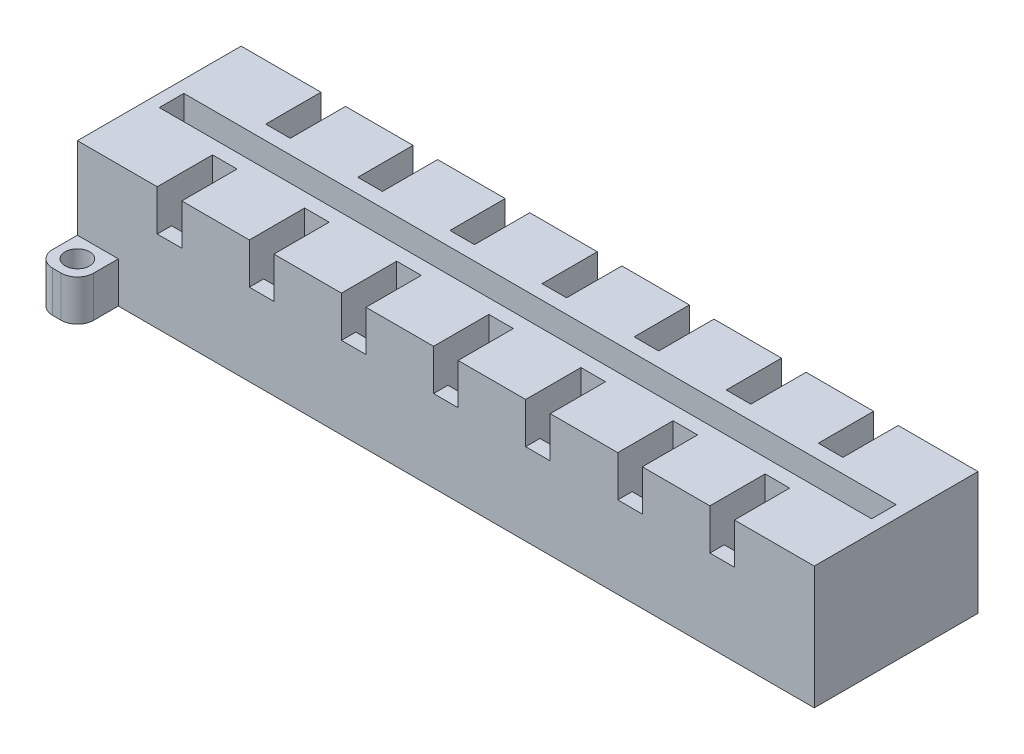
SolidWorks part; units mm, degrees
ref_plane "Front Plane" through (0, 0, 0) normal (0, 0, 1) x (1, 0, 0)
ref_plane "Top Plane" through (0, 0, 0) normal (0, 1, 0) x (1, 0, 0)
ref_plane "Right Plane" through (0, 0, 0) normal (1, 0, 0) x (0, 0, -1)
sketch "Sketch1" plane through (0, 0, 0) normal (0, 0, 1) x (1, 0, 0)
  line L1 (0, 0) -> (90, 0)
  line L2 (0, 0) -> (0, -20)
  line L3 (0, -20) -> (90, -20)
  line L4 (90, 0) -> (90, -20)
  dimension "D1" = 20
  dimension "D2" = 90
extrude "Boss-Extrude1" add sketch "Sketch1" along normal blind 20
sketch "Sketch2" plane through (0, 0, 0) normal (0, 1, 0) x (1, 0, 0)
  line L0 (0, -10) -> (90, -10) construction
  line L1 (0, -20) -> (0, 0) construction
  line L2 (90, -20) -> (90, 0) construction
  line L4 (0, -8.5) -> (90, -8.5)
  line L5 (0, -8.5) -> (0, -11.5)
  line L6 (0, -11.5) -> (90, -11.5)
  line L7 (90, -8.5) -> (90, -11.5)
  line L8 (0, -8.5) -> (90, -11.5) construction
  line L9 (0, -11.5) -> (90, -8.5) construction
  point P6 (45, -10)
  dimension "D1" = 3
extrude "Cut-Extrude1" cut sketch "Sketch2" against normal blind 10
sketch "Sketch3" plane through (0, 0, 0) normal (0, 1, 0) x (1, 0, 0)
  line L0 (45, 0) -> (45, -20) construction
  line L1 (90, 0) -> (0, 0) construction
  line L2 (90, -20) -> (0, -20) construction
  line L3 (45, -20) -> (90, -20) construction
  line L4 (90, -20) -> (90, 0) construction
  line L5 (90, 0) -> (45, 0) construction
  line L6 (45, 0) -> (0, 0) construction
  line L7 (0, 0) -> (0, -20) construction
  line L8 (0, -20) -> (45, -20) construction
  line L9 (45, -20) -> (22.5, -20) construction
  line L10 (22.5, -20) -> (22.5, 0) construction
  line L11 (22.5, 0) -> (67.5, 0) construction
  line L12 (67.5, 0) -> (67.5, -20) construction
  line L13 (22.5, 0) -> (0, 0) construction
  line L14 (0, 0) -> (11.25, 0) construction
  line L15 (11.25, 0) -> (11.25, -20) construction
  line L16 (11.25, -20) -> (22.5, -20) construction
  line L17 (22.5, -20) -> (45, -20) construction
  line L18 (45, -20) -> (33.75, -20) construction
  line L19 (33.75, -20) -> (33.75, 0) construction
  line L20 (33.75, 0) -> (45, 0) construction
  line L21 (45, 0) -> (67.5, 0) construction
  line L22 (67.5, 0) -> (56.25, 0) construction
  line L23 (56.25, 0) -> (56.25, -20) construction
  line L24 (56.25, -20) -> (67.5, -20) construction
  line L25 (67.5, -20) -> (90, -20) construction
  line L26 (78.75, -20) -> (78.75, 0) construction
  line L27 (0, -11.5) -> (0, -20) construction
  line L28 (0, -20) -> (0, -15.75) construction
  line L29 (0, -15.75) -> (90, -15.75) construction
  line L30 (90, -15.75) -> (90, 0) construction
  line L31 (90, 0) -> (90, -8.5) construction
  line L32 (90, -8.5) -> (90, -4.25) construction
  line L33 (90, -4.25) -> (0, -4.25) construction
  line L35 (9.75, -13.25) -> (12.75, -13.25)
  line L36 (9.75, -13.25) -> (9.75, -18.25)
  line L37 (9.75, -18.25) -> (12.75, -18.25)
  line L38 (12.75, -13.25) -> (12.75, -18.25)
  line L39 (9.75, -13.25) -> (12.75, -18.25) construction
  line L40 (9.75, -18.25) -> (12.75, -13.25) construction
  line L41 (21, -13.25) -> (24, -13.25)
  line L42 (21, -13.25) -> (21, -18.25)
  line L43 (21, -18.25) -> (24, -18.25)
  line L44 (24, -13.25) -> (24, -18.25)
  line L45 (21, -13.25) -> (24, -18.25) construction
  line L46 (21, -18.25) -> (24, -13.25) construction
  line L47 (32.25, -13.25) -> (35.25, -13.25)
  line L48 (32.25, -13.25) -> (32.25, -18.25)
  line L49 (32.25, -18.25) -> (35.25, -18.25)
  line L50 (35.25, -13.25) -> (35.25, -18.25)
  line L51 (32.25, -13.25) -> (35.25, -18.25) construction
  line L52 (32.25, -18.25) -> (35.25, -13.25) construction
  line L53 (43.5, -13.25) -> (46.5, -13.25)
  line L54 (43.5, -13.25) -> (43.5, -18.25)
  line L55 (43.5, -18.25) -> (46.5, -18.25)
  line L56 (46.5, -13.25) -> (46.5, -18.25)
  line L57 (43.5, -13.25) -> (46.5, -18.25) construction
  line L58 (43.5, -18.25) -> (46.5, -13.25) construction
  line L59 (54.75, -13.25) -> (57.75, -13.25)
  line L60 (54.75, -13.25) -> (54.75, -18.25)
  line L61 (54.75, -18.25) -> (57.75, -18.25)
  line L62 (57.75, -13.25) -> (57.75, -18.25)
  line L63 (54.75, -13.25) -> (57.75, -18.25) construction
  line L64 (54.75, -18.25) -> (57.75, -13.25) construction
  line L65 (66, -13.25) -> (69, -13.25)
  line L66 (66, -13.25) -> (66, -18.25)
  line L67 (66, -18.25) -> (69, -18.25)
  line L68 (69, -13.25) -> (69, -18.25)
  line L69 (66, -13.25) -> (69, -18.25) construction
  line L70 (66, -18.25) -> (69, -13.25) construction
  line L71 (77.25, -13.25) -> (80.25, -13.25)
  line L72 (77.25, -13.25) -> (77.25, -18.25)
  line L73 (77.25, -18.25) -> (80.25, -18.25)
  line L74 (80.25, -13.25) -> (80.25, -18.25)
  line L75 (77.25, -13.25) -> (80.25, -18.25) construction
  line L76 (77.25, -18.25) -> (80.25, -13.25) construction
  line L77 (9.75, -1.75) -> (12.75, -1.75)
  line L78 (9.75, -1.75) -> (9.75, -6.75)
  line L79 (9.75, -6.75) -> (12.75, -6.75)
  line L80 (12.75, -1.75) -> (12.75, -6.75)
  line L81 (9.75, -1.75) -> (12.75, -6.75) construction
  line L82 (9.75, -6.75) -> (12.75, -1.75) construction
  line L83 (21, -1.75) -> (24, -1.75)
  line L84 (21, -1.75) -> (21, -6.75)
  line L85 (21, -6.75) -> (24, -6.75)
  line L86 (24, -1.75) -> (24, -6.75)
  line L87 (21, -1.75) -> (24, -6.75) construction
  line L88 (21, -6.75) -> (24, -1.75) construction
  line L89 (32.25, -1.75) -> (35.25, -1.75)
  line L90 (32.25, -1.75) -> (32.25, -6.75)
  line L91 (32.25, -6.75) -> (35.25, -6.75)
  line L92 (35.25, -1.75) -> (35.25, -6.75)
  line L93 (32.25, -1.75) -> (35.25, -6.75) construction
  line L94 (32.25, -6.75) -> (35.25, -1.75) construction
  line L95 (43.5, -1.75) -> (46.5, -1.75)
  line L96 (43.5, -1.75) -> (43.5, -6.75)
  line L97 (43.5, -6.75) -> (46.5, -6.75)
  line L98 (46.5, -1.75) -> (46.5, -6.75)
  line L99 (43.5, -1.75) -> (46.5, -6.75) construction
  line L100 (43.5, -6.75) -> (46.5, -1.75) construction
  line L101 (54.75, -1.75) -> (57.75, -1.75)
  line L102 (54.75, -1.75) -> (54.75, -6.75)
  line L103 (54.75, -6.75) -> (57.75, -6.75)
  line L104 (57.75, -1.75) -> (57.75, -6.75)
  line L105 (54.75, -1.75) -> (57.75, -6.75) construction
  line L106 (54.75, -6.75) -> (57.75, -1.75) construction
  line L107 (66, -1.75) -> (69, -1.75)
  line L108 (66, -1.75) -> (66, -6.75)
  line L109 (66, -6.75) -> (69, -6.75)
  line L110 (69, -1.75) -> (69, -6.75)
  line L111 (66, -1.75) -> (69, -6.75) construction
  line L112 (66, -6.75) -> (69, -1.75) construction
  line L113 (77.25, -1.75) -> (80.25, -1.75)
  line L114 (77.25, -1.75) -> (77.25, -6.75)
  line L115 (77.25, -6.75) -> (80.25, -6.75)
  line L116 (80.25, -1.75) -> (80.25, -6.75)
  line L117 (77.25, -1.75) -> (80.25, -6.75) construction
  line L118 (77.25, -6.75) -> (80.25, -1.75) construction
  point P27 (11.25, -15.75)
  point P39 (22.5, -15.75)
  point P44 (33.75, -15.75)
  point P49 (45, -15.75)
  point P54 (56.25, -15.75)
  point P59 (67.5, -15.75)
  point P64 (78.75, -15.75)
  point P69 (11.25, -4.25)
  point P74 (22.5, -4.25)
  point P79 (33.75, -4.25)
  point P84 (45, -4.25)
  point P89 (56.25, -4.25)
  point P94 (67.5, -4.25)
  point P99 (78.75, -4.25)
  dimension "D1" = 3
  dimension "D2" = 3
  dimension "D3" = 3
  dimension "D4" = 3
  dimension "D5" = 3
  dimension "D6" = 3
  dimension "D7" = 3
  dimension "D8" = 5
  dimension "D9" = 5
  dimension "D10" = 5
  dimension "D11" = 5
  dimension "D12" = 5
  dimension "D13" = 5
  dimension "D14" = 5
  dimension "D15" = 5
  dimension "D16" = 5
  dimension "D17" = 5
  dimension "D18" = 5
  dimension "D19" = 5
  dimension "D20" = 5
  dimension "D21" = 5
extrude "Cut-Extrude2" cut sketch "Sketch3" against normal blind 10
sketch "Sketch4" plane through (0, 0, 0) normal (0, 1, 0) x (1, 0, 0)
  line L0 (90, -20) -> (0, -20) construction
  line L1 (9.75, -18.25) -> (12.75, -18.25)
  line L2 (9.75, -18.25) -> (9.75, -20)
  line L3 (9.75, -20) -> (12.75, -20)
  line L4 (12.75, -18.25) -> (12.75, -20)
  line L5 (90, 0) -> (0, 0) construction
  line L8 (21, -18.25) -> (24, -18.25)
  line L10 (21, -18.25) -> (24, -18.25)
  line L11 (21, -18.25) -> (21, -20)
  line L12 (21, -20) -> (24, -20)
  line L13 (24, -18.25) -> (24, -20)
  line L14 (32.25, -18.25) -> (35.2476, -18.25)
  line L15 (32.25, -18.25) -> (32.25, -20)
  line L16 (32.25, -20) -> (35.2476, -20)
  line L17 (35.2476, -18.25) -> (35.2476, -20)
  line L18 (43.5, -18.25) -> (46.5, -18.25)
  line L22 (46.5, -18.25) -> (43.5, -18.25)
  line L23 (46.5, -18.25) -> (46.5, -20)
  line L24 (46.5, -20) -> (43.5, -20)
  line L25 (43.5, -18.25) -> (43.5, -20)
  line L26 (54.75, -18.25) -> (57.75, -18.25)
  line L30 (57.75, -18.25) -> (54.75, -18.25)
  line L31 (57.75, -18.25) -> (57.75, -20)
  line L32 (57.75, -20) -> (54.75, -20)
  line L33 (54.75, -18.25) -> (54.75, -20)
  line L34 (66, -18.25) -> (69, -18.25)
  line L35 (66, -18.25) -> (66, -20)
  line L36 (66, -20) -> (69, -20)
  line L37 (69, -18.25) -> (69, -20)
  line L38 (77.25, -18.25) -> (80.2529, -18.25)
  line L39 (77.25, -18.25) -> (77.25, -20)
  line L40 (77.25, -20) -> (80.2529, -20)
  line L41 (80.2529, -18.25) -> (80.2529, -20)
  line L42 (9.75, -1.75) -> (12.75, -1.75)
  line L43 (9.75, -1.75) -> (9.75, 0)
  line L44 (9.75, 0) -> (12.75, 0)
  line L45 (12.75, -1.75) -> (12.75, 0)
  line L47 (21, -1.75) -> (24, -1.75)
  line L48 (21, -1.75) -> (21, 0)
  line L49 (21, 0) -> (24, 0)
  line L50 (24, -1.75) -> (24, 0)
  line L51 (32.25, -1.75) -> (35.2476, -1.75)
  line L52 (32.25, -1.75) -> (32.25, 0)
  line L53 (32.25, 0) -> (35.2476, 0)
  line L54 (35.2476, -1.75) -> (35.2476, 0)
  line L55 (43.5, -1.75) -> (46.5, -1.75)
  line L56 (43.5, -1.75) -> (43.5, 0)
  line L57 (43.5, 0) -> (46.5, 0)
  line L58 (46.5, -1.75) -> (46.5, 0)
  line L59 (54.75, -1.75) -> (57.75, -1.75)
  line L60 (54.75, -1.75) -> (54.75, 0)
  line L61 (54.75, 0) -> (57.75, 0)
  line L62 (57.75, -1.75) -> (57.75, 0)
  line L63 (66, -1.75) -> (69, -1.75)
  line L64 (66, -1.75) -> (66, 0)
  line L65 (66, 0) -> (69, 0)
  line L66 (69, -1.75) -> (69, 0)
  line L67 (77.25, -1.75) -> (80.2529, -1.75)
  line L68 (77.25, -1.75) -> (77.25, 0)
  line L69 (77.25, 0) -> (80.2529, 0)
  line L70 (80.2529, -1.75) -> (80.2529, 0)
  line M7 (80.25, -18.25) -> (77.25, -18.25)
  line M11 (69, -18.25) -> (66, -18.25)
  line M15 (57.75, -18.25) -> (54.75, -18.25)
  line M19 (46.5, -18.25) -> (43.5, -18.25)
  line M23 (35.25, -18.25) -> (32.25, -18.25)
  line M27 (24, -18.25) -> (21, -18.25)
  line M31 (12.75, -18.25) -> (9.75, -18.25)
  line M36 (0, -20) -> (90, -20)
extrude "Cut-Extrude3" cut sketch "Sketch4" against normal blind 5 contours L33 L31 M15 M36 | L37 L35 M11 M36 | L41 L38 L39 M7 M36 | L25 L23 M19 M36 | L17 L15 M23 M36 | L13 L11 M27 M36 | L4 L2 M31 M36 | L47 L50 L49 L48 | L51 L54 L53 L52 | L55 L58 L57 L56 | L59 L62 L61 L60 | L63 L66 L65 L64 | L67 L70 L69 L68 | L45 L44 L43 L42
sketch "Sketch5" plane through (0, -10, 0) normal (0, 1, 0) x (1, 0, 0)
  line L0 (0, -11.5) -> (90, -11.5) construction
  line L1 (0, -8.5) -> (1.5, -8.5)
  line L2 (0, -8.5) -> (0, -11.5)
  line L3 (0, -11.5) -> (1.5, -11.5)
  line L4 (1.5, -8.5) -> (1.5, -11.5)
  line L5 (9.75, -1.75) -> (9.75, -6.75) construction
  line L6 (90, -8.5) -> (88.5, -8.5)
  line L7 (90, -8.5) -> (90, -11.5)
  line L8 (90, -11.5) -> (88.5, -11.5)
  line L9 (88.5, -8.5) -> (88.5, -11.5)
  line L10 (80.25, -6.75) -> (80.25, -1.75) construction
  dimension "D1" = 8.25
  dimension "D2" = 8.25
extrude "Boss-Extrude2" add sketch "Sketch5" along normal blind 10
sketch "Sketch6" plane through (0, 0, 20) normal (0, 0, 1) x (1, 0, 0)
  line L0 (90, -20) -> (90, 0) construction
  line L1 (0, 0) -> (90, 0)
  line L2 (0, 0) -> (0, -10)
  line L3 (0, -10) -> (90, -10)
  line L4 (90, 0) -> (90, -10)
  line L5 (0, -20) -> (90, -20) construction
  line L6 (0, -10) -> (90, -10)
  line L7 (0, -10) -> (0, -15)
  line L8 (0, -15) -> (90, -15)
  line L9 (90, -10) -> (90, -15)
  line L11 (0, -15) -> (90, -15)
  line L12 (0, -15) -> (0, -20)
  line L13 (0, -20) -> (90, -20)
  line L14 (90, -15) -> (90, -20)
  line M9 (0, 0) -> (0, -20)
  line M10 (0, -20) -> (90, -20)
  line M11 (90, -20) -> (90, 0)
  dimension "D1" = 10
  dimension "D2" = 5
extrude "Cut-Extrude4" cut sketch "Sketch6" against normal blind 56 contours L8 M9 M10 M11
sketch "Sketch7" plane through (0, -15, 0) normal (0, -1, 0) x (1, 0, 0)
  line L1 (0, 20) -> (5, 20)
  line L2 (0, 20) -> (0, 25)
  line L3 (0, 25) -> (5, 25)
  line L4 (5, 20) -> (5, 25)
  line L5 (0, 0) -> (5, 0)
  line L6 (0, 0) -> (0, -5)
  line L7 (0, -5) -> (5, -5)
  line L8 (5, 0) -> (5, -5)
  dimension "D1" = 5
  dimension "D2" = 5
  dimension "D3" = 5
extrude "Boss-Extrude3" add sketch "Sketch7" against normal blind 5
sketch "Sketch8" plane through (0, -10, 0) normal (0, 1, 0) x (1, 0, 0)
  line L0 (2.5, 5) -> (2.5, -25) construction
  line L1 (0, 5) -> (5, 5) construction
  line L2 (5, -25) -> (0, -25) construction
  line L3 (0, 2.5) -> (5, 2.5) construction
  line L4 (0, 0) -> (0, 5) construction
  line L5 (5, 5) -> (5, 0) construction
  line L6 (5, 2.5) -> (5, -22.5) construction
  line L7 (5, -20) -> (5, -25) construction
  line L8 (5, -22.5) -> (0, -22.5) construction
  line L9 (0, -25) -> (0, -20) construction
  circle A0 centre (2.5, 2.5) radius 1.5
  circle A1 centre (2.5, -22.5) radius 1.5
  dimension "D1" = 3
  dimension "D2" = 3
extrude "Cut-Extrude5" cut sketch "Sketch8" against normal blind 5
fillet "Fillet3" radius 1.98 4 edges at (0, -12.5, 25) (0, -12.5, -5) (5, -12.5, -5) (5, -12.5, 25)
